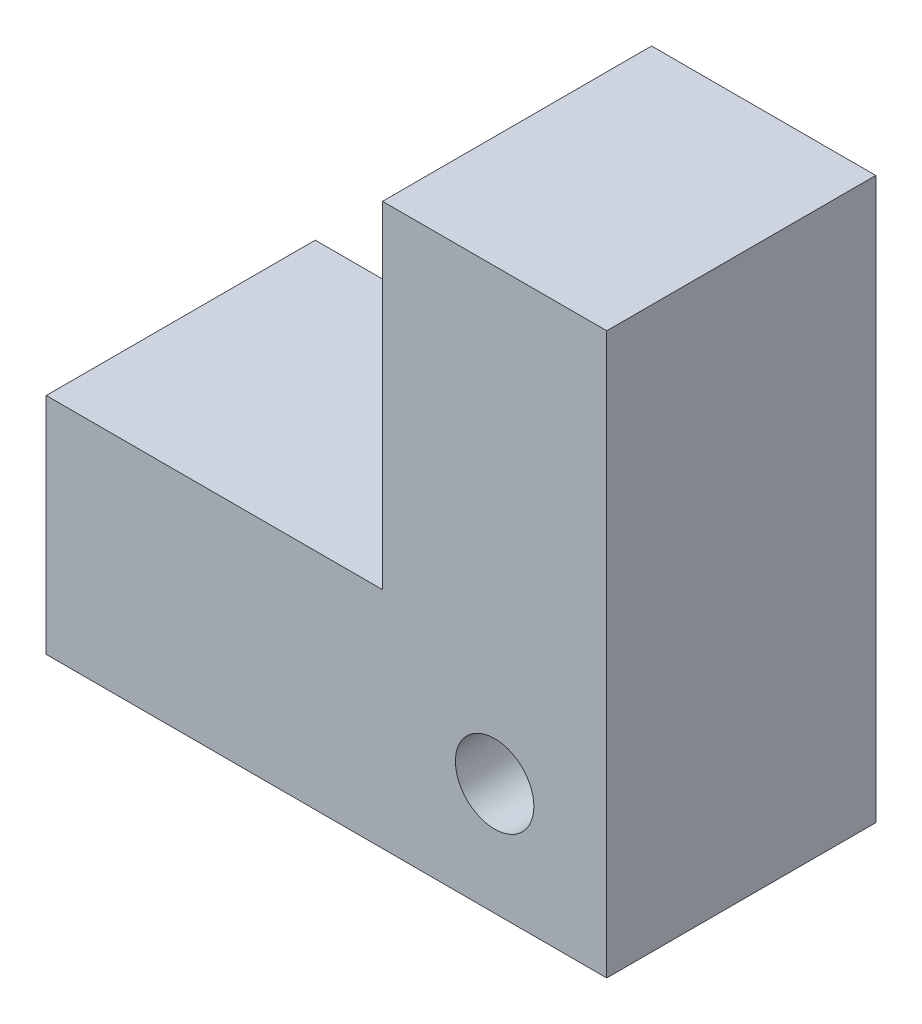
SolidWorks part; units mm, degrees
ref_plane "Front Plane" through (0, 0, 0) normal (0, 0, 1) x (1, 0, 0)
ref_plane "Top Plane" through (0, 0, 0) normal (0, 1, 0) x (1, 0, 0)
ref_plane "Right Plane" through (0, 0, 0) normal (1, 0, 0) x (0, 0, -1)
sketch "Sketch1" plane through (0, 0, 0) normal (0, 0, 1) x (1, 0, 0)
  line L0 (0, 0) -> (0, 25)
  line L1 (0, 25) -> (-10, 25)
  line L2 (-10, 25) -> (-10, 10)
  line L3 (-10, 10) -> (-25, 10)
  line L4 (-25, 10) -> (-25, 0)
  line L5 (-25, 0) -> (0, 0)
  dimension "D1" = 25
  dimension "D2" = 25
  dimension "D3" = 10
  dimension "D4" = 10
extrude "Boss-Extrude1" add sketch "Sketch1" along normal blind 12
sketch "Sketch2" plane through (0, 0, 12) normal (0, 0, 1) x (1, 0, 0)
  circle A0 centre (-5, 5) radius 1.75 construction
  circle A1 centre (-5, 5) radius 1.75
extrude "Cut-Extrude1" cut sketch "Sketch2" against normal through all
